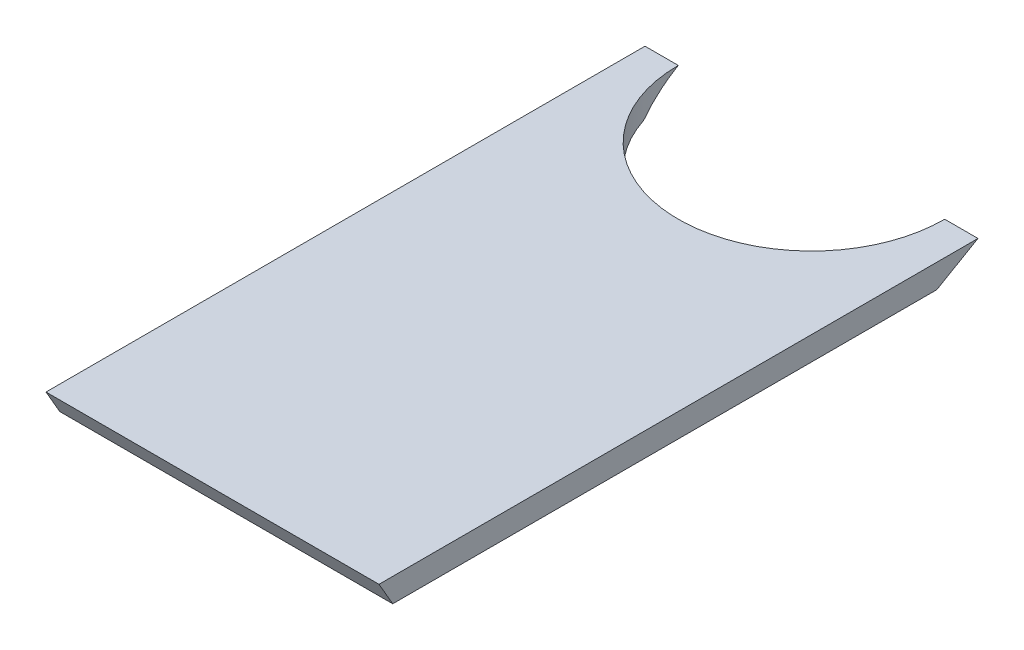
SolidWorks part; units mm, degrees
material "Maple"
ref_plane "Front Plane" through (0, 0, 0) normal (0, 0, 1) x (1, 0, 0)
ref_plane "Top Plane" through (0, 0, 0) normal (0, 1, 0) x (1, 0, 0)
ref_plane "Right Plane" through (0, 0, 0) normal (1, 0, 0) x (0, 0, -1)
sketch "Sketch3" plane through (0, 0, 0) normal (1, 0, 0) x (0, 0, -1)
  line L0 (-88.8255, 3.175) -> (-85.1593, -3.175)
  line L1 (-88.8255, 3.175) -> (71.0819, 3.175)
  line L3 (-85.1593, -3.175) -> (60.0834, -3.175)
  line L4 (25.7639, -195.2996) -> (-118.6986, 54.9168) construction
  line L7 (71.0819, 3.175) -> (60.0834, -3.175)
  line L9 (116.1292, 29.1831) -> (-48.8486, -66.0669) construction
  point P0 (0, 0)
  dimension "D1" = 6.35
extrude "Boss-Extrude1" add sketch "Sketch3" along normal mid plane 88.9
sketch "Sketch5" plane through (0, 3.175, 0) normal (0, 1, 0) x (1, 0, 0)
  line L0 (44.45, 71.0819) -> (-44.45, 71.0819) construction
  line L1 (44.45, 71.0819) -> (-44.45, 71.0819)
  line L2 (-35.56, 71.0819) -> (35.56, 71.0819)
  arc A0 (35.56, 71.0819) -> (-35.56, 71.0819) centre (0, 71.0819) cw
  dimension "D1" = 35.56
extrude "Cut-Extrude1" cut sketch "Sketch5" against normal through all contours A0 L1
